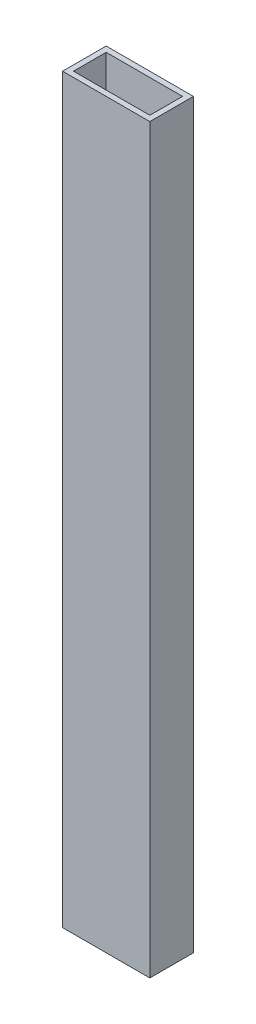
SolidWorks part; units mm, degrees
ref_plane "Front Plane" through (0, 0, 0) normal (0, 0, 1) x (1, 0, 0)
ref_plane "Top Plane" through (0, 0, 0) normal (0, 1, 0) x (1, 0, 0)
ref_plane "Right Plane" through (0, 0, 0) normal (1, 0, 0) x (0, 0, -1)
sketch "Sketch1" plane through (0, 0, 0) normal (0, 1, 0) x (1, 0, 0)
  line L1 (0, 0) -> (50.8, 0)
  line L2 (0, 0) -> (0, 25.4)
  line L3 (0, 25.4) -> (50.8, 25.4)
  line L4 (50.8, 0) -> (50.8, 25.4)
  line L5 (3.175, 22.225) -> (47.625, 22.225)
  line L6 (3.175, 22.225) -> (3.175, 3.175)
  line L7 (3.175, 3.175) -> (47.625, 3.175)
  line L8 (47.625, 22.225) -> (47.625, 3.175)
  dimension "D1" = 3.175
  dimension "D2" = 3.175
  dimension "D3" = 3.175
  dimension "D4" = 3.175
  dimension "D5" = 50.8
  dimension "D6" = 25.4
extrude "Boss-Extrude1" add sketch "Sketch1" along normal blind 431.8
